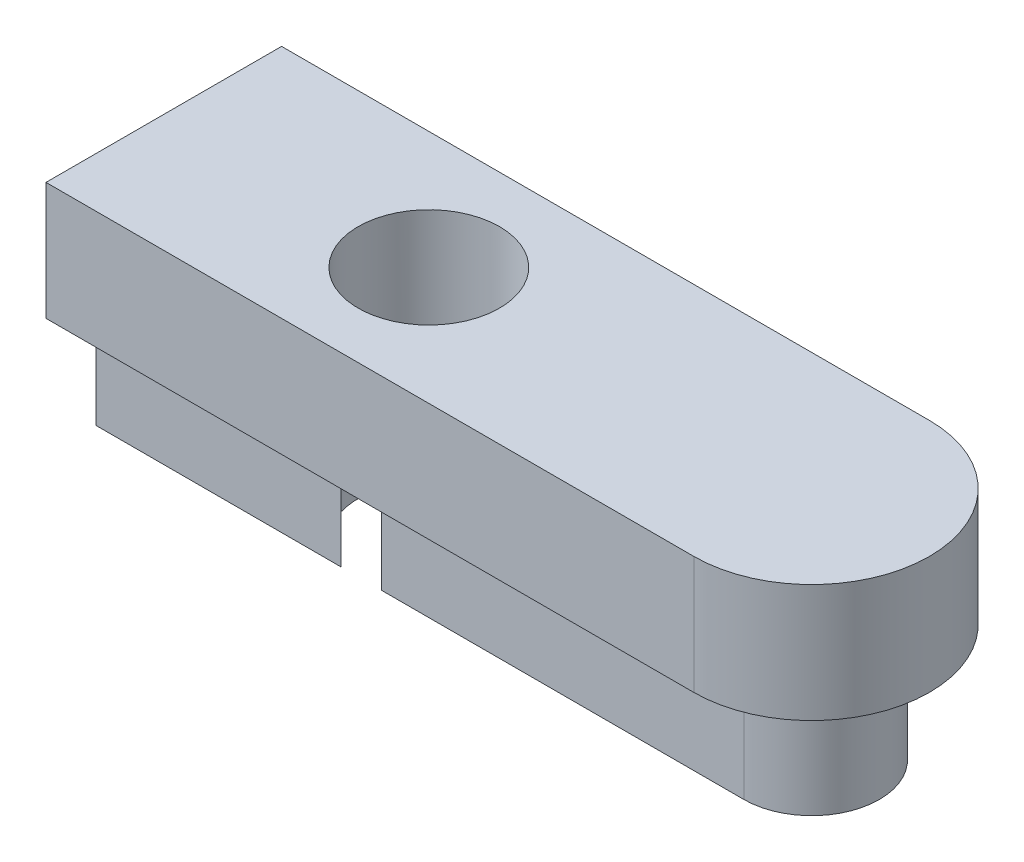
SolidWorks part; units mm, degrees
ref_plane "Front Plane" through (0, 0, 0) normal (0, 0, 1) x (1, 0, 0)
ref_plane "Top Plane" through (0, 0, 0) normal (0, 1, 0) x (1, 0, 0)
ref_plane "Right Plane" through (0, 0, 0) normal (1, 0, 0) x (0, 0, -1)
sketch "Sketch1" plane through (0, 0, 0) normal (0, 1, 0) x (1, 0, 0)
  line L0 (-6.5, 0) -> (6.5, 0) construction
  line L1 (-6.5, 2) -> (6.5, 2)
  line L2 (-6.5, -2) -> (6.5, -2)
  arc A0 (-6.5, 2) -> (-6.5, -2) centre (-6.5, 0) ccw
  arc A1 (6.5, -2) -> (6.5, 2) centre (6.5, 0) ccw
  point P2 (0, 0)
  dimension "D1" = 13
  dimension "D2" = 4
extrude "Boss-Extrude1" add sketch "Sketch1" along normal blind 2
sketch "Sketch2" plane through (0, 0, 0) normal (0, -1, 0) x (1, 0, 0)
  line L0 (-6.5, 0) -> (6.5, 0) construction
  line L1 (-6.5, 1.15) -> (6.5, 1.15)
  line L2 (-6.5, -1.15) -> (6.5, -1.15)
  line L3 (6.5, 1.2) -> (-6.5, 1.2) construction
  arc A0 (-6.5, 1.15) -> (-6.5, -1.15) centre (-6.5, 0) ccw
  arc A1 (6.5, -1.15) -> (6.5, 1.15) centre (6.5, 0) ccw
  point P2 (0, 0)
  dimension "D2" = 13
  dimension "D1" = 0.05
extrude "Boss-Extrude2" add sketch "Sketch2" along normal blind 2
sketch "Sketch3" plane through (0, -2, 0) normal (0, -1, 0) x (1, 0, 0)
  circle A0 centre (0, 0) radius 1.2
  dimension "D1" = 2.4
extrude "Cut-Extrude1" cut sketch "Sketch3" against normal through all
sketch "Sketch4" plane through (0, -2, 0) normal (0, -1, 0) x (1, 0, 0)
  line L0 (-4.5, -4.2) -> (-4.5, -1.2) construction
  line L1 (-4.5, -3) -> (-10.5, -3)
  line L2 (-4.5, -3) -> (-4.5, 3)
  line L3 (-4.5, 3) -> (-10.5, 3)
  line L4 (-10.5, -3) -> (-10.5, 3)
  point P6 (-4.5, 0)
  dimension "D1" = 6
extrude "Cut-Extrude2" cut sketch "Sketch4" against normal through all
